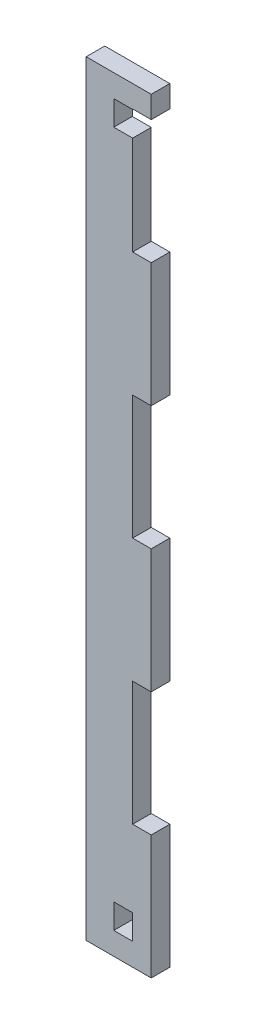
SolidWorks part; units mm, degrees
ref_plane "Face" through (0, 0, 0) normal (0, 0, 1) x (1, 0, 0)
ref_plane "Dessus" through (0, 0, 0) normal (0, 1, 0) x (1, 0, 0)
ref_plane "Droite" through (0, 0, 0) normal (1, 0, 0) x (0, 0, -1)
sketch "Esquisse1" plane through (0, 0, 0) normal (0, 0, 1) x (1, 0, 0)
  line L0 (6, 181.4099) -> (0, 181.4099) construction
  line L1 (-15, 181.4099) -> (6, 181.4099)
  line L2 (-15, 181.4099) -> (-15, -65.6932)
  line L3 (-15, -65.6932) -> (6, -65.6932)
  line L4 (6, 181.4099) -> (6, 174.308)
  line L5 (-15, -65.6938) -> (-15, 181.4099) construction
  line L6 (0, 14.3068) -> (0, -25.692) construction
  line L7 (0, -25.692) -> (6, -25.692) construction
  line L8 (0, -58.4432) -> (-2, -58.4432) construction
  line L9 (6, 14.3068) -> (0, 14.3068) construction
  line L11 (0, 54.3086) -> (6, 54.3086) construction
  line L13 (6, 94.3074) -> (0, 94.3074) construction
  line L14 (0, 174.308) -> (0, 134.3092) construction
  line L15 (0, 134.3092) -> (6, 134.3092) construction
  line L16 (0, 94.3074) -> (0, 54.3086)
  line L17 (6, 174.308) -> (0, 174.308) construction
  line L18 (0, 14.3068) -> (0, -25.692)
  line L19 (0, -25.692) -> (6, -25.692)
  line L21 (6, 14.3068) -> (0, 14.3068)
  line L23 (0, 54.3086) -> (6, 54.3086)
  line L25 (6, 94.3074) -> (0, 94.3074)
  line L26 (0, 174.308) -> (0, 174.1599)
  line L27 (0, 134.3092) -> (6, 134.3092)
  line L29 (6, 174.308) -> (0, 174.308)
  line L30 (6, 134.3092) -> (6, 94.3074)
  line L31 (6, 54.3086) -> (6, 14.3068)
  line L32 (6, -25.692) -> (6, -65.6932)
  line L33 (0, -58.4432) -> (0, -50.4432) construction
  line L34 (0, -50.4432) -> (-2, -50.4432) construction
  line L35 (0, -58.4432) -> (-6.1, -58.4432)
  line L36 (0, -58.4432) -> (0, -50.4432)
  line L37 (0, -50.4432) -> (-6.1, -50.4432)
  line L38 (0, 174.1599) -> (-2, 174.1599) construction
  line L40 (0, 166.1599) -> (-2, 166.1599) construction
  line L43 (0, 166.1599) -> (-6.1, 166.1599)
  line L44 (0, 174.1599) -> (-6.1, 174.1599)
  line L45 (-6.1, 166.1599) -> (-6.1, 174.1599)
  line L46 (0, 166.1599) -> (0, 134.3092)
  line L47 (-6.1, -50.4432) -> (-6.1, -58.4432)
  dimension "D1" = 6.1
extrude "Boss.-Extru.1" add sketch "Esquisse1" along normal blind 6
